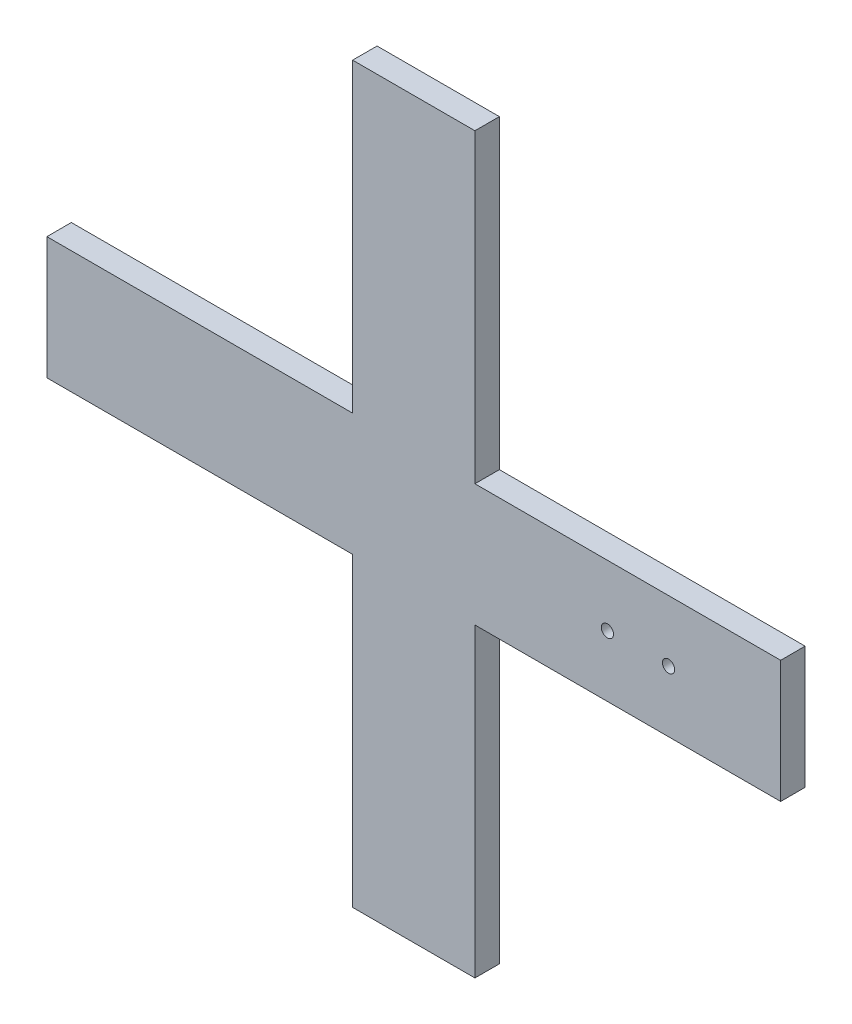
SolidWorks part; units mm, degrees
ref_plane "Plano frontal" through (0, 0, 0) normal (0, 0, 1) x (1, 0, 0)
ref_plane "Plano superior" through (0, 0, 0) normal (0, 1, 0) x (1, 0, 0)
ref_plane "Plano direito" through (0, 0, 0) normal (1, 0, 0) x (0, 0, -1)
sketch "Esboço1" plane through (0, 0, 0) normal (0, 0, 1) x (1, 0, 0)
  line L0 (105, 180) -> (105, 105)
  line L1 (0, 0) -> (180, 0)
  line L2 (0, 0) -> (0, 180)
  line L3 (0, 180) -> (180, 180)
  line L4 (180, 0) -> (180, 180)
  line L5 (0, 180) -> (75, 180)
  line L6 (0, 180) -> (0, 105)
  line L7 (0, 105) -> (75, 105)
  line L8 (75, 180) -> (75, 105)
  line L9 (105, 180) -> (180, 180)
  line L10 (180, 180) -> (180, 105)
  line L11 (105, 105) -> (180, 105)
  line L12 (105, 75) -> (105, 0)
  line L13 (105, 75) -> (180, 75)
  line L14 (180, 75) -> (180, 0)
  line L15 (105, 0) -> (180, 0)
  line L16 (0, 75) -> (0, 0)
  line L17 (0, 75) -> (75, 75)
  line L18 (75, 75) -> (75, 0)
  line L19 (0, 0) -> (75, 0)
  line L20 (0, 90) -> (180, 90) construction
  line L21 (90, 90) -> (137.5, 90) construction
  line L22 (137.5, 90) -> (152.5, 90) construction
  line L23 (90, 180) -> (90, 0) construction
  circle A2 centre (137.5, 90) radius 1.5
  circle A3 centre (152.5, 90) radius 1.5
  dimension "D6" = 3
  dimension "D8" = 3
  dimension "D1" = 180
  dimension "D2" = 75
  dimension "D3" = 2
  dimension "D5" = 47.5
  dimension "D7" = 15
  dimension "D4" = 2
extrude "Ressalto-extrusão1" add sketch "Esboço1" along normal blind 6 contours L17 L18 L1 L12 L13 L4 L11 L0 L3 L8 L7 L2
